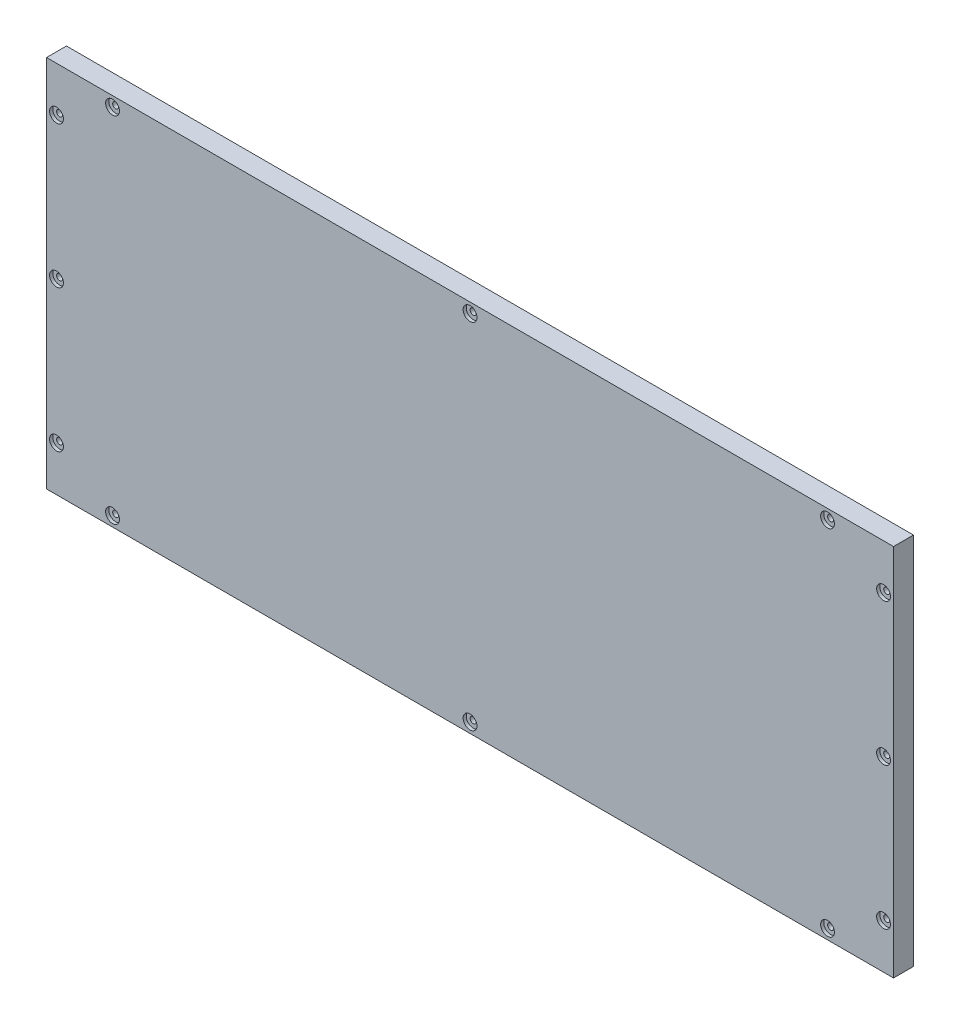
SolidWorks part; units mm, degrees
ref_plane "Front Plane" through (0, 0, 0) normal (0, 0, 1) x (1, 0, 0)
ref_plane "Top Plane" through (0, 0, 0) normal (0, 1, 0) x (1, 0, 0)
ref_plane "Right Plane" through (0, 0, 0) normal (1, 0, 0) x (0, 0, -1)
sketch "Sketch1" plane through (0, 0, 0) normal (0, 0, 1) x (1, 0, 0)
  line L1 (0, 0) -> (340, 0)
  line L2 (0, 0) -> (0, 150)
  line L3 (0, 150) -> (340, 150)
  line L4 (340, 0) -> (340, 150)
  dimension "D1" = 340
  dimension "D2" = 150
extrude "Boss-Extrude1" add sketch "Sketch1" along normal blind 8
sketch "Sketch2" plane through (0, 0, 8) normal (0, 0, 1) x (1, 0, 0)
  line L0 (16.5, 150) -> (16.5, 0)
  line L1 (340, 150) -> (0, 150) construction
  line L2 (0, 0) -> (340, 0) construction
  line L3 (0, 150) -> (0, 0) construction
  line L4 (0, 142) -> (340, 142)
  line L5 (340, 0) -> (340, 150) construction
  line L6 (0, 8) -> (340, 8)
  line L7 (323.5, 150) -> (323.5, 0)
  dimension "D1" = 16.5
  dimension "D2" = 8
  dimension "D3" = 8
  dimension "D4" = 16.5
hole_wizard "CBORE for #2 Binding Head Machine Screw1" positions "Sketch3" profile "Sketch4" counterbore size "#2" standard "ANSI Inch"
sketch "Sketch3" plane through (0, 0, 8) normal (0, 0, 1) x (1, 0, 0)
  line L0 (16.5, 150) -> (16.5, 0) construction
  line L2 (0, 142) -> (340, 142) construction
  line L3 (0, 8) -> (340, 8) construction
  line L4 (0, 0) -> (340, 0) construction
  line L5 (323.5, 150) -> (323.5, 0) construction
  line L7 (340, 0) -> (340, 150) construction
  line L8 (0, 150) -> (0, 0) construction
  line L9 (340, 150) -> (0, 150) construction
  point P0 (4, 132)
  point P2 (4, 75)
  point P4 (4, 18)
  point P6 (26.5, 4)
  point P8 (170, 4)
  point P10 (313.5, 4)
  point P12 (336, 18)
  point P14 (336, 75)
  point P16 (336, 132)
  point P18 (313.5, 146)
  point P20 (170, 146)
  point P22 (26.5, 146)
  point P36 (170, 0)
  point P55 (340, 75)
  point P56 (170, 142)
  point P66 (0, 75)
  dimension "D2" = 10
  dimension "D3" = 4
  dimension "D4" = 0
  dimension "D5" = 10
  dimension "D6" = 4
  dimension "D7" = 10
  dimension "D8" = 0
  dimension "D9" = 4
  dimension "D10" = 4
  dimension "D11" = 10
  dimension "D12" = 10
  dimension "D13" = 4
  dimension "D14" = 4
  dimension "D15" = 0
  dimension "D16" = 10
  dimension "D17" = 4
  dimension "D18" = 10
  dimension "D19" = 4
  dimension "D20" = 0
  dimension "D21" = 4
  dimension "D22" = 10
  dimension "D23" = 4
  dimension "D24" = 4
  dimension "D25" = 4
sketch "Sketch4" plane through (4, 132, 8) normal (1, 0, 0) x (0, -1, 0)
  line L0 (0, 0) -> (0, 20.7326)
  line L1 (0, 20.7326) -> (1.2192, 20)
  line L2 (1.2192, 20) -> (1.2192, 1.27)
  line L3 (1.2192, 1.27) -> (2.7788, 1.27)
  line L4 (2.7788, 1.27) -> (2.7788, 0)
  line L5 (2.7788, 0) -> (0, 0)
  line L10 (0, 20.7326) -> (-1.2192, 20) construction
  line L11 (0, -6.35) -> (0, 107.95) construction
  dimension "Hole Dia." = 2.4384
  dimension "Hole Depth" = 20
  dimension "C'Bore Dia." = 5.5575
  dimension "C'Bore Depth" = 1.27
  dimension "Drill Angle" = 118
